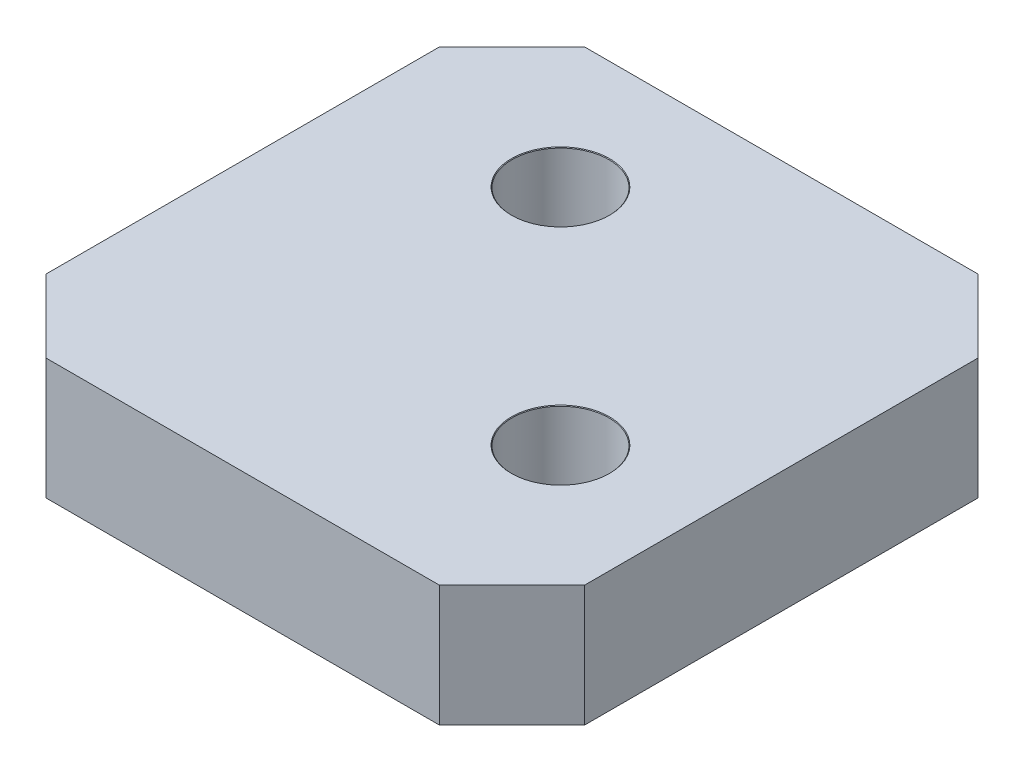
SolidWorks part; units mm, degrees
ref_plane "Front Plane" through (0, 0, 0) normal (0, 0, 1) x (1, 0, 0)
ref_plane "Top Plane" through (0, 0, 0) normal (0, 1, 0) x (1, 0, 0)
ref_plane "Right Plane" through (0, 0, 0) normal (1, 0, 0) x (0, 0, -1)
sketch "Sketch1" plane through (0, 0, 0) normal (0, 1, 0) x (1, 0, 0)
  line L0 (-11.3223, 17.145) -> (41.0428, 17.145) construction
  line L1 (0, 0) -> (22.225, 0)
  line L2 (0, 0) -> (0, 22.225)
  line L3 (0, 22.225) -> (22.225, 22.225)
  line L4 (22.225, 0) -> (22.225, 22.225)
  line L5 (17.145, 32.1525) -> (17.145, -4.5703) construction
  line L6 (9.779, 28.0598) -> (9.779, -2.9444) construction
  line L7 (-4.8747, 9.779) -> (36.2212, 9.779) construction
  point P13 (17.145, 9.779)
  point P14 (9.779, 17.145)
  dimension "D1" = 22.225
  dimension "D2" = 22.225
  dimension "D3" = 9.779
  dimension "D4" = 9.779
  dimension "D5" = 5.08
  dimension "D6" = 5.08
extrude "Boss-Extrude1" add sketch "Sketch1" along normal blind 5
sketch "Sketch2" plane through (0, 5, 0) normal (0, 1, 0) x (1, 0, 0)
  line L0 (7.5, 7.5) -> (7.5, 16.725) construction
  line L1 (7.5, 16.725) -> (16.725, 16.725) construction
  line L2 (16.725, 16.725) -> (16.725, 7.5) construction
  line L3 (16.725, 7.5) -> (7.5, 7.5) construction
  line L4 (0, 0) -> (22.225, 0) construction
  line L5 (0, 22.225) -> (0, 0) construction
  line L6 (22.225, 0) -> (22.225, 22.225) construction
  line L7 (22.225, 22.225) -> (0, 22.225) construction
  point P13 (7.5, 16.725)
  point P14 (16.725, 7.5)
  dimension "D1" = 7.5
  dimension "D2" = 7.5
  dimension "D3" = 5.5
  dimension "D4" = 5.5
hole_wizard "Ø4.0mm Dowel Hole3" positions "Sketch3" profile "Sketch4" hole size "Ø4.0" standard "ANSI Metric" end condition through all
sketch "Sketch3" plane through (0, 5, 0) normal (0, 1, 0) x (1, 0, 0)
  point P0 (7.5, 16.725)
  point P3 (16.725, 7.5)
sketch "Sketch4" plane through (7.5, 5, -16.725) normal (1, 0, 0) x (0, 0, 1)
  line L0 (0, 0) -> (0, 5)
  line L1 (0, 5) -> (2, 5)
  line L2 (2, 5) -> (2, 0.025)
  line L3 (2, 0.025) -> (2.025, 0)
  line L5 (2.025, 0) -> (0, 0)
  line L6 (-2, 0.025) -> (-2.025, 0) construction
  line L11 (0, -6.35) -> (0, 107.95) construction
  dimension "Thru Hole Dia." = 4
  dimension "Thru Hole Depth" = 5
  dimension "Near C'Sink Dia." = 4.05
  dimension "Near C'Sink Angle" = 90
chamfer "Chamfer1" distance 3 angle 45 4 edges at (0, 2.5, 0) (22.225, 2.5, 0) (22.225, 2.5, -22.225) (0, 2.5, -22.225)
